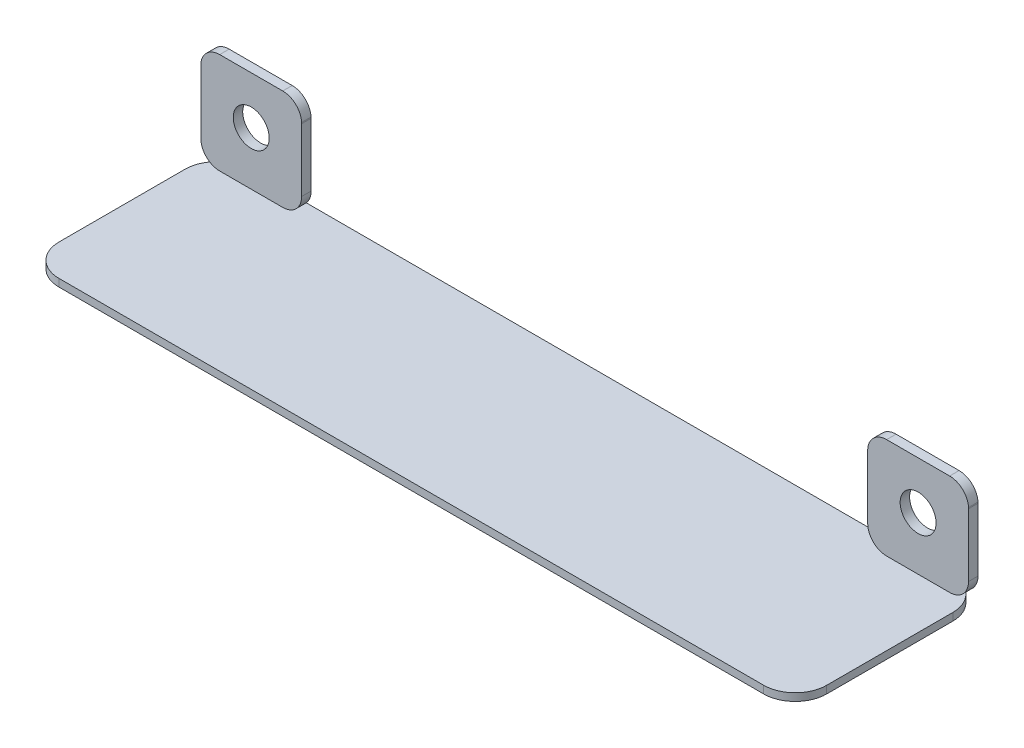
SolidWorks part; units mm, degrees
ref_plane "Front Plane" through (0, 0, 0) normal (0, 0, 1) x (1, 0, 0)
ref_plane "Top Plane" through (0, 0, 0) normal (0, 1, 0) x (1, 0, 0)
ref_plane "Right Plane" through (0, 0, 0) normal (1, 0, 0) x (0, 0, -1)
sketch "Sketch3" plane through (0, 0, 0) normal (0, 0, 1) x (1, 0, 0)
  line L6 (-7.9975, -43.2281) -> (-8, -43.4)
  line L7 (-8, -43.4) -> (-8, -53.4)
  line L8 (-5, -56.4) -> (5, -56.4)
  line L9 (8, -53.4) -> (8, -43.4)
  line L10 (8, -43.4) -> (7.9975, -43.2281)
  line L11 (5, -40.4) -> (-5, -40.4)
  line L12 (-7.9975, -43.2281) -> (-8, -43.4)
  line L13 (-8, -43.4) -> (-8, -53.4)
  line L14 (-5, -56.4) -> (5, -56.4)
  line L15 (8, -53.4) -> (8, -43.4)
  line L16 (8, -43.4) -> (7.9975, -43.2281)
  line L17 (5, -40.4) -> (-5, -40.4)
  line L18 (110.8, -40.4) -> (100.8, -40.4)
  line L19 (97.8025, -43.2281) -> (97.8, -43.4)
  line L20 (97.8, -43.4) -> (97.8, -53.4)
  line L21 (100.8, -56.4) -> (110.8, -56.4)
  line L22 (113.8, -53.4) -> (113.8, -43.4)
  line L23 (113.8, -43.4) -> (113.7975, -43.2281)
  line L24 (110.8, -40.4) -> (100.8, -40.4)
  line L25 (97.8025, -43.2281) -> (97.8, -43.4)
  line L26 (97.8, -43.4) -> (97.8, -53.4)
  line L27 (100.8, -56.4) -> (110.8, -56.4)
  line L28 (113.8, -53.4) -> (113.8, -43.4)
  line L29 (113.8, -43.4) -> (113.7975, -43.2281)
  circle A0 centre (0, -47.9524) radius 2.85 construction
  circle A1 centre (0, -47.9524) radius 2.85
  arc A2 (-5, -40.4) -> (-7.9975, -43.2281) centre (-5.0013, -43.4012) ccw
  arc A3 (-8, -53.4) -> (-5, -56.4) centre (-5, -53.4) ccw
  arc A4 (5, -56.4) -> (8, -53.4) centre (5, -53.4) ccw
  arc A5 (7.9975, -43.2281) -> (5, -40.4) centre (5.0013, -43.4012) ccw
  arc A6 (-5, -40.4) -> (-7.9975, -43.2281) centre (-5.0013, -43.4012) ccw
  arc A7 (-8, -53.4) -> (-5, -56.4) centre (-5, -53.4) ccw
  arc A8 (5, -56.4) -> (8, -53.4) centre (5, -53.4) ccw
  arc A9 (7.9975, -43.2281) -> (5, -40.4) centre (5.0013, -43.4012) ccw
  circle A10 centre (105.8, -47.9524) radius 2.85 construction
  circle A11 centre (105.8, -47.9524) radius 2.85
  arc A12 (100.8, -40.4) -> (97.8025, -43.2281) centre (100.7987, -43.4012) ccw
  arc A13 (97.8, -53.4) -> (100.8, -56.4) centre (100.8, -53.4) ccw
  arc A14 (110.8, -56.4) -> (113.8, -53.4) centre (110.8, -53.4) ccw
  arc A15 (113.7975, -43.2281) -> (110.8, -40.4) centre (110.8013, -43.4012) ccw
  arc A16 (100.8, -40.4) -> (97.8025, -43.2281) centre (100.7987, -43.4012) ccw
  arc A17 (97.8, -53.4) -> (100.8, -56.4) centre (100.8, -53.4) ccw
  arc A18 (110.8, -56.4) -> (113.8, -53.4) centre (110.8, -53.4) ccw
  arc A19 (113.7975, -43.2281) -> (110.8, -40.4) centre (110.8013, -43.4012) ccw
  dimension "D1" = 0
  dimension "D2" = 0
extrude "Boss-Extrude3" add sketch "Sketch3" along normal up to surface (1.5 mm away)
sketch "Sketch2" plane through (0, -56.4, 0) normal (0, -1, 0) x (1, 0, 0)
  line L1 (-8, -1) -> (113.8, -1)
  line L2 (-8, -1) -> (-8, 29)
  line L3 (-8, 29) -> (113.8, 29)
  line L4 (113.8, -1) -> (113.8, 29)
  line L5 (113.8, 0) -> (113.8, -78.8637) construction
  line L6 (-8, -78.8637) -> (-8, 0) construction
  line L9 (-5, 0) -> (-8, 0) construction
  dimension "D1" = 30
  dimension "D2" = 121.8
  dimension "D3" = 1
extrude "Boss-Extrude2" add sketch "Sketch2" along normal blind 1.2
fillet "Fillet1" radius 5 4 edges at (113.8, -57, 29) (113.8, -57, -1) (-8, -57, -1) (-8, -57, 29)
